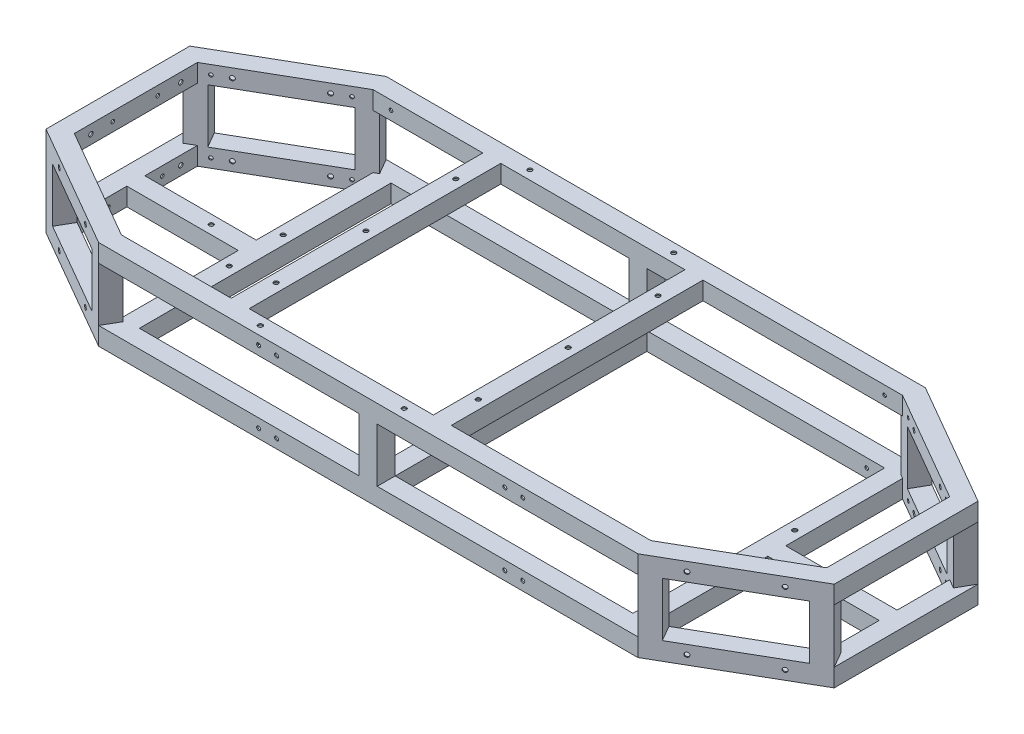
SolidWorks part; units mm, degrees
material "6061-T6 (SS)"
ref_plane "Front Plane" through (0, 0, 0) normal (0, 0, 1) x (1, 0, 0)
ref_plane "Top Plane" through (0, 0, 0) normal (0, 1, 0) x (1, 0, 0)
ref_plane "Right Plane" through (0, 0, 0) normal (1, 0, 0) x (0, 0, -1)
sketch "Sketch2" plane through (0, 0, 0) normal (1, 0, 0) x (0, 0, -1)
  line L0 (179.451, -11.049) -> (179.451, 11.049)
  line L5 (179.451, 11.049) -> (201.549, 11.049)
  line L6 (201.549, -11.049) -> (201.549, 11.049)
  line L7 (177.8, -12.7) -> (203.2, -12.7)
  line L8 (177.8, -12.7) -> (177.8, 12.7)
  line L9 (177.8, 12.7) -> (203.2, 12.7)
  line L10 (203.2, -12.7) -> (203.2, 12.7)
  line L11 (177.8, -12.7) -> (203.2, 12.7) construction
  line L12 (177.8, 12.7) -> (203.2, -12.7) construction
  line L13 (179.451, -11.049) -> (201.549, -11.049)
  point P5 (190.5, 0)
  dimension "D1" = 25.4
  dimension "D3" = 203.2
  dimension "D2" = 1.651
sketch "Sketch3" plane through (0, 0, 0) normal (0, 1, 0) x (1, 0, 0)
  line L0 (-381, 203.2) -> (381, 203.2)
  line L1 (0, 177.8) -> (0, 203.2) construction
  line L2 (0, 177.8) -> (0, 203.2) construction
  line L3 (381, 203.2) -> (556.9764, 101.6)
  line L4 (556.9764, 101.6) -> (556.9764, -101.6)
  line L5 (556.9764, -101.6) -> (381, -203.2)
  line L8 (381, -203.2) -> (-381, -203.2)
  line L9 (0, -203.2) -> (0, 203.2) construction
  line L10 (0, 0) -> (556.9764, 0) construction
  line L11 (-556.9764, -101.6) -> (-381, -203.2)
  line L12 (-556.9764, 101.6) -> (-556.9764, -101.6)
  line L13 (-381, 203.2) -> (-556.9764, 101.6)
  dimension "D1" = 762
  dimension "D2" = 30
  dimension "D3" = 203.2
  dimension "D4" = 203.2
  dimension "D5" = 203.2
  dimension "D6" = 30
sweep "Bottom Frame" add profiles "Sketch2" path "Sketch3"
sketch "Sketch4" plane through (0, 12.7, 0) normal (0, 1, 0) x (1, 0, 0)
  line L0 (-381, -203.2) -> (-402.997, -190.5)
  line L1 (-381, -203.2) -> (-556.9764, -101.6) construction
  line L2 (-402.997, -190.5) -> (-390.297, -168.503)
  line L3 (-374.1941, -177.8) -> (-531.5764, -86.9353) construction
  line L4 (-390.297, -168.503) -> (-368.3, -181.203)
  line L5 (-368.3, -181.203) -> (-381, -203.2)
  line L6 (-381.6043, -200.9447) -> (-400.7417, -189.8957)
  line L7 (-400.7417, -189.8957) -> (-389.6927, -170.7583)
  line L8 (-389.6927, -170.7583) -> (-370.5553, -181.8073)
  line L9 (-370.5553, -181.8073) -> (-381.6043, -200.9447)
  dimension "D2" = 1.651
  dimension "D1" = 25.4
extrude "Vertical Member 1" add sketch "Sketch4" along normal blind 76.2
sketch "Sketch5" plane through (0, 12.7, 0) normal (0, 1, 0) x (1, 0, 0)
  line L0 (-556.9764, -101.6) -> (-534.9793, -114.3)
  line L1 (-402.997, -190.5) -> (-556.9764, -101.6) construction
  line L2 (-534.9793, -114.3) -> (-522.2793, -92.303)
  line L3 (-390.297, -168.503) -> (-531.5764, -86.9353) construction
  line L4 (-522.2793, -92.303) -> (-544.2764, -79.603)
  line L5 (-544.2764, -79.603) -> (-556.9764, -101.6)
  line L6 (-554.7211, -100.9957) -> (-535.5836, -112.0447)
  line L7 (-535.5836, -112.0447) -> (-524.5346, -92.9073)
  line L8 (-524.5346, -92.9073) -> (-543.6721, -81.8583)
  line L9 (-543.6721, -81.8583) -> (-554.7211, -100.9957)
  dimension "D2" = 1.651
  dimension "D1" = 25.4
extrude "Vertical Member 2" add sketch "Sketch5" along normal blind 76.2
mirror "Vertical Member 3 & 4" about plane through (0, 0, 0) normal (0, 0, 1) of "Vertical Member 1", "Vertical Member 2"
mirror "Vertical Members 5, 6, 7, 8" about plane through (0, 0, 0) normal (1, 0, 0) of "Vertical Member 3 & 4", "Vertical Member 1", "Vertical Member 2"
sketch "Sketch6" plane through (0, 12.7, 0) normal (0, 1, 0) x (1, 0, 0)
  line L0 (0, 0) -> (0, -203.2) construction
  line L1 (381, -203.2) -> (-381, -203.2) construction
  line L8 (374.1941, -177.8) -> (-374.1941, -177.8) construction
  line L9 (-12.7, -203.2) -> (12.7, -203.2)
  line L10 (-12.7, -203.2) -> (-12.7, -177.8)
  line L11 (-12.7, -177.8) -> (12.7, -177.8)
  line L12 (12.7, -203.2) -> (12.7, -177.8)
  line L13 (-11.049, -201.549) -> (-11.049, -179.451)
  line L14 (-11.049, -179.451) -> (11.049, -179.451)
  line L15 (11.049, -201.549) -> (11.049, -179.451)
  line L16 (-11.049, -201.549) -> (11.049, -201.549)
  point P11 (0, -203.2)
  dimension "D2" = 1.651
  dimension "D1" = 25.4
extrude "Middle Vertical Member 1" add sketch "Sketch6" along normal blind 88.9
mirror "Middle Vertical Member 2" about plane through (0, 0, 0) normal (0, 0, 1) of "Middle Vertical Member 1"
ref_plane "Top Frame Mirror Plane" through (0, 50.8, 0) normal (0, 1, 0) x (1, 0, 0)
mirror "Top Frame" about plane through (0, 50.8, 0) normal (0, 1, 0) of "Bottom Frame"
sketch "Sketch7" plane through (0, 0, 177.8) normal (0, 0, -1) x (-1, 0, 0)
  line L7 (12.7, 88.9) -> (12.7, 12.7) construction
  line L8 (-12.7, 12.7) -> (12.7, 12.7)
  line L9 (-12.7, 12.7) -> (-12.7, -12.7)
  line L10 (-12.7, -12.7) -> (12.7, -12.7)
  line L11 (12.7, 12.7) -> (12.7, -12.7)
  line L12 (-11.049, 11.049) -> (-11.049, -11.049)
  line L13 (-11.049, -11.049) -> (11.049, -11.049)
  line L14 (11.049, 11.049) -> (11.049, -11.049)
  line L15 (-11.049, 11.049) -> (11.049, 11.049)
  dimension "D2" = 1.651
  dimension "D1" = 25.4
extrude "Middle Support" add sketch "Sketch7" along normal up to surface (355.6 mm away)
sketch "Sketch8" plane through (0, 0, 177.8) normal (0, 0, -1) x (-1, 0, 0)
  line L0 (12.7, -12.7) -> (374.1941, -12.7) construction
  line L1 (374.1941, 12.7) -> (348.7941, 12.7)
  line L2 (374.1941, 12.7) -> (374.1941, -12.7)
  line L3 (374.1941, -12.7) -> (348.7941, -12.7)
  line L4 (348.7941, 12.7) -> (348.7941, -12.7)
  line L5 (372.5431, 11.049) -> (372.5431, -11.049)
  line L6 (372.5431, -11.049) -> (350.4451, -11.049)
  line L7 (350.4451, 11.049) -> (350.4451, -11.049)
  line L8 (372.5431, 11.049) -> (350.4451, 11.049)
  dimension "D2" = 1.651
  dimension "D1" = 25.4
extrude "Bottom Support Rear" add sketch "Sketch8" along normal up to surface (355.6 mm away) up to face at (193.447, 0, -177.8)
sketch "Sketch9" plane through (-531.5764, 0, 0) normal (1, 0, 0) x (0, 0, -1)
  line L0 (-86.9353, 12.7) -> (86.9353, 12.7) construction
  line L1 (-12.7, 12.7) -> (12.7, 12.7)
  line L2 (-12.7, 12.7) -> (-12.7, -12.7)
  line L3 (-12.7, -12.7) -> (12.7, -12.7)
  line L4 (12.7, 12.7) -> (12.7, -12.7)
  line L5 (-86.9353, -12.7) -> (86.9353, -12.7) construction
  line L6 (-11.049, 11.049) -> (-11.049, -11.049)
  line L7 (-11.049, -11.049) -> (11.049, -11.049)
  line L8 (11.049, 11.049) -> (11.049, -11.049)
  line L9 (-11.049, 11.049) -> (11.049, 11.049)
  point P6 (0, -12.7)
  dimension "D2" = 1.651
  dimension "D1" = 25.4
extrude "I Beam" add sketch "Sketch9" along normal up to surface (157.3823 mm away) up to face at (-374.1941, 0, 0)
mirror "Bottom Support Front w/ I Beam" about plane through (0, 0, 0) normal (1, 0, 0) of "Bottom Support Rear", "I Beam"
sketch "Sketch10" plane through (0, 0, 177.8) normal (0, 0, -1) x (-1, 0, 0)
  line L0 (195.326, 90.551) -> (195.326, 112.649)
  line L1 (193.675, 88.9) -> (219.075, 88.9)
  line L2 (193.675, 88.9) -> (193.675, 114.3)
  line L3 (193.675, 114.3) -> (219.075, 114.3)
  line L4 (219.075, 88.9) -> (219.075, 114.3)
  line L5 (193.675, 88.9) -> (219.075, 114.3) construction
  line L6 (193.675, 114.3) -> (219.075, 88.9) construction
  line L7 (195.326, 112.649) -> (217.424, 112.649)
  line L8 (217.424, 90.551) -> (217.424, 112.649)
  line L9 (195.326, 90.551) -> (217.424, 90.551)
  line L10 (374.1941, 114.3) -> (-374.1941, 114.3) construction
  line L11 (374.1941, 88.9) -> (12.7, 88.9) construction
  point P0 (206.375, 101.6)
  dimension "D2" = 1.651
  dimension "D1" = 25.4
  dimension "D3" = 206.375
extrude "Top Rear Support" add sketch "Sketch10" along normal up to surface (355.6 mm away) up to face at (180.747, 0, -177.8)
ref_plane "Top Support Plane" through (-63.5, 0, 0) normal (1, 0, 0) x (0, 0, -1)
mirror "Top Front Support" about plane through (-63.5, 0, 0) normal (1, 0, 0) of "Top Rear Support"
sketch "Top Rear Support Holes" plane through (0, 114.3, 0) normal (0, 1, 0) x (1, 0, 0)
  line L0 (-206.375, 127) -> (-206.375, -127) construction
  line L1 (-219.075, 177.8) -> (-219.075, -177.8) construction
  point P4 (-206.375, 0)
  point P5 (-219.075, 0)
  dimension "D1" = 254
  dimension "D2" = 12.7
hole_wizard "1/4 (0.25) Diameter Hole 1" positions "Sketch12" profile "Sketch13" hole size "1/4" standard "ANSI Inch" end condition through all
sketch "Sketch12" plane through (0, 114.3, 0) normal (0, 1, 0) x (1, 0, 0)
  point P0 (-206.375, 127)
  point P3 (-206.375, -127)
  point P6 (-206.375, 0)
sketch "Sketch13" plane through (-206.375, 114.3, -127) normal (1, 0, 0) x (0, 0, 1)
  line L0 (0, 0) -> (0, 127)
  line L1 (0, 127) -> (3.175, 127)
  line L2 (3.175, 127) -> (3.175, 0)
  line L5 (3.175, 0) -> (0, 0)
  line L11 (0, -6.35) -> (0, 107.95) construction
  dimension "Thru Hole Dia." = 6.35
  dimension "Thru Hole Depth" = 127
mirror "1/4 (0.25) Diameter Hole 2" about plane through (-63.5, 0, 0) normal (1, 0, 0) of "1/4 (0.25) Diameter Hole 1"
sketch "Right SIde Holes" plane through (0, 114.3, 0) normal (0, 1, 0) x (1, 0, 0)
  line L0 (-165.1, -190.5) -> (38.1, -190.5) construction
  line L1 (-193.675, -177.8) -> (66.675, -177.8) construction
  point P2 (-63.5, -190.5)
  dimension "D1" = 203.2
  dimension "D2" = 63.5
  dimension "D3" = 12.7
hole_wizard "1/4 (0.25) Diameter Hole 3" positions "Sketch15" profile "Sketch17" hole size "1/4" standard "ANSI Inch"
sketch "Sketch15" plane through (0, 114.3, 0) normal (0, 1, 0) x (1, 0, 0)
  point P0 (-165.1, -190.5)
  point P3 (38.1, -190.5)
sketch "Sketch17" plane through (-165.1, 114.3, 190.5) normal (1, 0, 0) x (0, 0, 1)
  line L0 (0, 0) -> (0, 52.7077)
  line L1 (0, 52.7077) -> (3.175, 50.8)
  line L2 (3.175, 50.8) -> (3.175, 0)
  line L5 (3.175, 0) -> (0, 0)
  line L10 (0, 52.7077) -> (-3.175, 50.8) construction
  line L11 (0, -6.35) -> (0, 107.95) construction
  dimension "Hole Dia." = 6.35
  dimension "Hole Depth" = 50.8
  dimension "Drill Angle" = 118
mirror "1/4 (0.25) Diameter Hole 4" about plane through (0, 0, 0) normal (0, 0, 1) of "1/4 (0.25) Diameter Hole 3"
sketch "Hole Location" plane through (-183.2382, 0, 317.3778) normal (-0.5, 0, 0.866) x (0.866, 0, 0.5)
  line L0 (-380.7557, 101.6) -> (-279.1557, 101.6) construction
  line L1 (-406.1557, 88.9) -> (-253.7557, 88.9) construction
  point P4 (-329.9557, 101.6)
  point P5 (-329.9557, 88.9)
  dimension "D1" = 101.6
  dimension "D2" = 12.7
hole_wizard "1/4 (0.25) Diameter Hole3" positions "Sketch19" profile "Sketch20" hole size "1/4" standard "ANSI Inch"
sketch "Sketch19" plane through (-183.2382, 0, 317.3778) normal (-0.5, 0, 0.866) x (0.866, 0, 0.5)
  point P0 (-380.7557, 101.6)
  point P3 (-279.1557, 101.6)
sketch "Sketch20" plane through (-512.9823, 101.6, 127) normal (0, 1, 0) x (0.866, 0, 0.5)
  line L0 (0, 0) -> (0, 52.7077)
  line L1 (0, 52.7077) -> (3.175, 50.8)
  line L2 (3.175, 50.8) -> (3.175, 0)
  line L5 (3.175, 0) -> (0, 0)
  line L10 (0, 52.7077) -> (-3.175, 50.8) construction
  line L11 (0, -6.35) -> (0, 107.95) construction
  dimension "Hole Dia." = 6.35
  dimension "Hole Depth" = 50.8
  dimension "Drill Angle" = 118
mirror "Hole Location 1" about plane through (0, 50.8, 0) normal (0, 1, 0) of "1/4 (0.25) Diameter Hole3"
mirror "Hole Location 2" about plane through (0, 0, 0) normal (0, 0, 1) of "Hole Location 1", "1/4 (0.25) Diameter Hole3"
mirror "Hole Location 3" about plane through (0, 0, 0) normal (1, 0, 0) of "Hole Location 2", "1/4 (0.25) Diameter Hole3", "Hole Location 1"
sketch "Sketch22" plane through (-170.5382, 0, -295.3808) normal (0.5, 0, 0.866) x (0.866, 0, -0.5)
  line L0 (-402.9807, 101.6) -> (-256.9307, 101.6) construction
  line L2 (-329.9557, 88.9) -> (-329.9557, 114.3) construction
  line L3 (-253.7557, 88.9) -> (-406.1557, 88.9) construction
  line L4 (-235.1616, 114.3) -> (-416.891, 114.3) construction
  circle A0 centre (-402.9807, 101.6) radius 2.54
  circle A1 centre (-256.9307, 101.6) radius 2.54
  point P9 (-329.9557, 101.6)
  dimension "D2" = 5.08
  dimension "D3" = 5.08
  dimension "D1" = 146.05
extrude "Inner Hole Location 1" cut sketch "Sketch22" against normal blind 6.35
mirror "Inner Hole Location 2" about plane through (0, 50.8, 0) normal (0, 1, 0) of "Inner Hole Location 1"
mirror "Inner Hole Location 3" about plane through (0, 0, 0) normal (0, 0, 1) of "Inner Hole Location 2", "Inner Hole Location 1"
mirror "Inner Hole Location 4" about plane through (0, 0, 0) normal (1, 0, 0) of "Inner Hole Location 3", "Inner Hole Location 1", "Inner Hole Location 2"
sketch "Sketch23" plane through (0, 12.7, 0) normal (0, 1, 0) x (1, 0, 0)
  line L1 (-374.1941, 12.7) -> (-531.5764, 12.7) construction
  line L2 (-374.1941, 177.8) -> (-374.1941, 12.7) construction
  line L3 (-374.1941, -177.8) -> (-219.075, -177.8) construction
  line L4 (-374.1941, -12.7) -> (-374.1941, -177.8) construction
  circle A0 centre (-424.9941, 0) radius 3.175
  circle A1 centre (-361.4941, -38.1) radius 3.175
  circle A2 centre (-361.4941, 38.1) radius 3.175
  dimension "D1" = 6.35
  dimension "D2" = 12.7
  dimension "D3" = 50.8
  dimension "D4" = 139.7
  dimension "D5" = 215.9
  dimension "D6" = 12.7
  dimension "D7" = 12.7
extrude "Rear Shock Mount Holes" cut sketch "Sketch23" against normal through all
mirror "Front Shock Mount Holes" about plane through (0, 0, 0) normal (1, 0, 0) of "Rear Shock Mount Holes"
sketch "Sketch24" plane through (0, 88.9, 0) normal (0, -1, 0) x (1, 0, 0)
  line L0 (-206.375, 130.175) -> (-206.375, 123.825) construction
  line L1 (-193.675, 177.8) -> (-12.7, 177.8) construction
  line L2 (-206.375, 3.175) -> (-206.375, -3.175) construction
  line L3 (-12.7, -177.8) -> (-193.675, -177.8) construction
  line L4 (-206.375, -123.825) -> (-206.375, -130.175) construction
  line L5 (66.675, 0) -> (-193.675, 0) construction
  line L6 (66.675, -177.8) -> (66.675, 177.8) construction
  line L7 (-193.675, -177.8) -> (-193.675, 177.8) construction
  line L8 (-63.5, 0) -> (-63.5, 177.8) construction
  circle A0 centre (-206.375, 139.7) radius 1.2446
  circle A1 centre (-206.375, 114.3) radius 1.2446
  circle A2 centre (-206.375, 127) radius 3.175 construction
  circle A3 centre (-206.375, 12.7) radius 1.2446
  circle A4 centre (-206.375, -12.7) radius 1.2446
  circle A5 centre (-206.375, 0) radius 3.175 construction
  circle A6 centre (-206.375, -114.3) radius 1.2446
  circle A7 centre (-206.375, -139.7) radius 1.2446
  circle A8 centre (-206.375, -127) radius 3.175 construction
  circle A9 centre (79.375, 139.7) radius 1.2446
  circle A10 centre (79.375, 114.3) radius 1.2446
  circle A11 centre (79.375, 12.7) radius 1.2446
  circle A12 centre (79.375, -12.7) radius 1.2446
  circle A13 centre (79.375, -114.3) radius 1.2446
  circle A14 centre (79.375, -139.7) radius 1.2446
  dimension "D1" = 2.4892
  dimension "D2" = 38.1
  dimension "D3" = 25.4
  dimension "D4" = 101.6
  dimension "D5" = 25.4
  dimension "D6" = 38.1
  dimension "D7" = 25.4
extrude "Z Direction Holes" cut sketch "Sketch24" against normal blind 1.651
sketch "Sketch25" plane through (0, 88.9, 0) normal (0, -1, 0) x (1, 0, 0)
  line L0 (-168.275, -190.5) -> (-161.925, -190.5) construction
  line L1 (66.675, 0) -> (-193.675, 0) construction
  line L2 (66.675, -177.8) -> (66.675, 177.8) construction
  line L3 (-193.675, -177.8) -> (-193.675, 177.8) construction
  line L4 (-63.5, 0) -> (-63.5, -177.8) construction
  line L5 (-12.7, -177.8) -> (-193.675, -177.8) construction
  circle A0 centre (-152.4, -190.5) radius 1.2446
  circle A1 centre (-177.8, -190.5) radius 1.2446
  circle A2 centre (-165.1, -190.5) radius 3.175 construction
  circle A3 centre (50.8, -190.5) radius 1.2446
  circle A4 centre (25.4, -190.5) radius 1.2446
  circle A5 centre (50.8, 190.5) radius 1.2446
  circle A6 centre (25.4, 190.5) radius 1.2446
  circle A7 centre (-177.8, 190.5) radius 1.2446
  circle A8 centre (-152.4, 190.5) radius 1.2446
  dimension "D1" = 2.4892
  dimension "D2" = 203.2
  dimension "D3" = 25.4
extrude "X Direction Holes" cut sketch "Sketch25" against normal blind 1.651
sketch "Sketch26" plane through (-556.9764, 0, 0) normal (-1, 0, 0) x (0, 0, 1)
  line L0 (-101.6, 88.9) -> (-101.6, 114.3) construction
  line L1 (-101.6, 114.3) -> (101.6, 114.3) construction
  line L2 (-101.6, 50.8) -> (101.6, 50.8) construction
  line L3 (-101.6, 88.9) -> (-101.6, 12.7) construction
  line L4 (101.6, 88.9) -> (101.6, 12.7) construction
  circle A0 centre (-63.5, 101.6) radius 3.175
  circle A1 centre (63.5, 101.6) radius 3.175
  circle A4 centre (63.5, 0) radius 3.175
  circle A5 centre (-63.5, 0) radius 3.175
  dimension "D1" = 6.35
  dimension "D2" = 38.1
  dimension "D3" = 127
  dimension "D4" = 12.7
extrude "Rear Holes" cut sketch "Sketch26" against normal blind 25.4
sketch "Sketch27" plane through (0, -12.7, 0) normal (0, -1, 0) x (1, 0, 0)
  line L1 (-348.7941, -177.8) -> (-348.7941, -203.2) construction
  line L4 (-381, -203.2) -> (381, -203.2) construction
  line L5 (-531.5764, -86.9353) -> (-556.9764, -86.9353) construction
  line L6 (-556.9764, 101.6) -> (-556.9764, -101.6) construction
  line L7 (531.5764, -86.9353) -> (556.9764, -86.9353) construction
  line L8 (556.9764, -101.6) -> (556.9764, 101.6) construction
  line L9 (-556.9764, 0) -> (556.9764, 0) construction
  circle A0 centre (-361.442, -190.5) radius 1.2446
  circle A1 centre (-243.078, -190.5) radius 1.2446
  circle A2 centre (-121.666, -190.5) radius 1.2446
  circle A3 centre (0, -190.5) radius 1.2446
  circle A4 centre (121.666, -190.5) radius 1.2446
  circle A5 centre (243.078, -190.5) radius 1.2446
  circle A6 centre (361.442, -190.5) radius 1.2446
  circle A7 centre (-544.2764, -94.234) radius 1.2446
  circle A8 centre (544.2764, -94.234) radius 1.2446
  circle A9 centre (544.2764, 94.234) radius 1.2446
  circle A10 centre (361.442, 190.5) radius 1.2446
  circle A11 centre (243.078, 190.5) radius 1.2446
  circle A12 centre (121.666, 190.5) radius 1.2446
  circle A13 centre (0, 190.5) radius 1.2446
  circle A14 centre (-121.666, 190.5) radius 1.2446
  circle A15 centre (-243.078, 190.5) radius 1.2446
  circle A16 centre (-361.442, 190.5) radius 1.2446
  circle A17 centre (-544.2764, 94.234) radius 1.2446
  point P20 (-348.7941, -190.5)
  point P29 (-544.2764, -86.9353)
  point P38 (544.2764, -86.9353)
  dimension "D1" = 2.4892
  dimension "D2" = 19.558
  dimension "D3" = 137.922
  dimension "D4" = 259.334
  dimension "D5" = 381
  dimension "D6" = 502.666
  dimension "D7" = 624.078
  dimension "D8" = 19.558
  dimension "D9" = 7.366
  dimension "D10" = 7.366
extrude "Cut-Extrude5" cut sketch "Sketch27" against normal blind 1.651
sketch "Sketch28" [suppressed] plane through (0, 0, -203.2) normal (0, 0, -1) x (-1, 0, 0)
  line L0 (-381, 101.6) -> (381, 101.6) construction
  line L1 (-381, 88.9) -> (-381, 114.3) construction
  line L2 (381, 88.9) -> (381, 114.3) construction
  line L3 (-381, 0) -> (381, 0) construction
  line L4 (-381, -12.7) -> (-381, 12.7) construction
  line L5 (381, -12.7) -> (381, 12.7) construction
  circle A0 centre (-252.73, 101.6) radius 3.3782
  circle A1 centre (-193.04, 101.6) radius 3.3782
  circle A2 centre (-218.44, 101.6) radius 3.3782
  circle A3 centre (-252.73, 0) radius 3.3782
  circle A4 centre (-218.44, 0) radius 3.3782
  circle A5 centre (-193.04, 0) radius 3.3782
  circle A6 centre (129.54, 101.6) radius 3.3782
  circle A7 centre (154.94, 101.6) radius 3.3782
  circle A8 centre (176.53, 101.6) radius 3.3782
  circle A9 centre (129.54, 0) radius 3.3782
  circle A10 centre (154.94, 0) radius 3.3782
  circle A11 centre (176.53, 0) radius 3.3782
  dimension "D4" = 6.7564
  dimension "D1" = 128.27
  dimension "D2" = 162.56
  dimension "D3" = 187.96
  dimension "D5" = 510.54
  dimension "D6" = 535.94
  dimension "D7" = 557.53
extrude "Cut-Extrude6" [suppressed] cut sketch "Sketch28" against normal blind 25.4
sketch "Sketch29" plane through (0, 0, 203.2) normal (0, 0, 1) x (1, 0, 0)
  line L0 (-381, 101.6) -> (381, 101.6) construction
  line L1 (-381, 88.9) -> (-381, 114.3) construction
  line L2 (381, 88.9) -> (381, 114.3) construction
  line L3 (-381, 0) -> (381, 0) construction
  line L4 (-381, -12.7) -> (-381, 12.7) construction
  line L5 (381, -12.7) -> (381, 12.7) construction
  circle A1 centre (-154.94, 101.6) radius 2.8067
  circle A2 centre (-129.54, 101.6) radius 2.8067
  circle A4 centre (-154.94, 0) radius 2.8067
  circle A5 centre (-129.54, 0) radius 2.8067
  circle A6 centre (193.04, 101.6) radius 2.8067
  circle A7 centre (218.44, 101.6) radius 2.8067
  circle A9 centre (193.04, 0) radius 2.8067
  circle A10 centre (218.44, 0) radius 2.8067
  dimension "D1" = 5.6134
  dimension "D3" = 226.06
  dimension "D4" = 251.46
  dimension "D5" = 574.04
  dimension "D6" = 599.44
extrude "Cut-Extrude7" cut sketch "Sketch29" against normal blind 25.4
sketch "Sketch30" plane through (0, 0, -177.8) normal (0, 0, 1) x (1, 0, 0)
  line L0 (374.1941, 114.3) -> (92.075, 114.3) construction
  line L1 (374.1941, 88.9) -> (374.1941, 114.3) construction
  line L2 (-219.075, 114.3) -> (-374.1941, 114.3) construction
  line L3 (-374.1941, 88.9) -> (-374.1941, 114.3) construction
  line L4 (-348.7941, -12.7) -> (-12.7, -12.7) construction
  line L5 (12.7, -12.7) -> (348.7941, -12.7) construction
  circle A0 centre (348.7941, 101.6) radius 2.54
  circle A1 centre (-348.7941, 101.6) radius 2.54
  circle A2 centre (-323.3941, 0) radius 2.54
  circle A3 centre (323.3941, 0) radius 2.54
  dimension "D1" = 5.08
  dimension "D2" = 12.7
  dimension "D3" = 25.4
  dimension "D4" = 12.7
  dimension "D5" = 25.4
  dimension "D6" = 50.8
  dimension "D7" = 12.7
  dimension "D8" = 50.8
  dimension "D9" = 12.7
extrude "Cut-Extrude8" cut sketch "Sketch30" against normal blind 1.651
mirror "Mirror1" about plane through (0, 0, 0) normal (0, 0, 1) of "Cut-Extrude8"
sketch "Sketch31" plane through (-531.5764, 0, 0) normal (1, 0, 0) x (0, 0, -1)
  line L0 (86.9353, 114.3) -> (-86.9353, 114.3) construction
  line L1 (-86.9353, 88.9) -> (-86.9353, 114.3) construction
  line L2 (-86.9353, 12.7) -> (-12.7, 12.7) construction
  line L3 (12.7, 12.7) -> (86.9353, 12.7) construction
  line L4 (-86.9353, -12.7) -> (-86.9353, 12.7) construction
  circle A0 centre (-32.5793, 101.6) radius 2.54
  circle A1 centre (30.9207, 101.6) radius 2.54
  circle A2 centre (-38.9293, 0) radius 2.54
  circle A3 centre (37.2707, 0) radius 2.54
  dimension "D1" = 5.08
  dimension "D2" = 12.7
  dimension "D3" = 54.356
  dimension "D4" = 63.5
  dimension "D5" = 12.7
  dimension "D6" = 12.7
  dimension "D7" = 12.7
  dimension "D8" = 48.006
  dimension "D9" = 76.2
extrude "Cut-Extrude9" cut sketch "Sketch31" against normal blind 1.651
mirror "Mirror2" about plane through (0, 0, 0) normal (1, 0, 0) of "Cut-Extrude9"
sketch "Sketch32" plane through (0, 114.3, 0) normal (0, 1, 0) x (1, 0, 0)
  line L0 (-219.075, 177.8) -> (-219.075, -177.8) construction
  line L1 (381, 203.2) -> (-381, 203.2) construction
  line L2 (-348.7941, 0) -> (-219.075, 0) construction
  line L3 (-348.7941, 177.8) -> (-348.7941, -177.8) construction
  circle A0 centre (-283.972, 190.5) radius 6.35
  circle A1 centre (-283.972, -190.5) radius 6.35
  dimension "D1" = 12.7
  dimension "D2" = 64.897
  dimension "D3" = 12.7
extrude "Cut-Extrude10" [suppressed] cut sketch "Sketch32" against normal through all
equation "\"Tubing\"= 1in"
equation "\"Wall Thickness\"= 0.065"
equation "\"D1@Sketch2\" = \"Tubing\""
equation "\"D2@Sketch2\"= \"Wall Thickness\""
equation "\"D1@Sketch4\"= \"Tubing\""
equation "\"D2@Sketch4\"= \"Wall Thickness\""
equation "\"D1@Sketch5\"= \"Tubing\""
equation "\"D2@Sketch5\"= \"Wall Thickness\""
equation "\"D1@Sketch6\"= \"Tubing\""
equation "\"D2@Sketch6\"= \"Wall Thickness\""
equation "\"D1@Sketch7\"= \"Tubing\""
equation "\"D2@Sketch7\"= \"Wall Thickness\""
equation "\"D1@Sketch8\"= \"Tubing\""
equation "\"D2@Sketch8\"= \"Wall Thickness\""
equation "\"D1@Sketch9\"= \"Tubing\""
equation "\"D2@Sketch9\"= \"Wall Thickness\""
equation "\"D1@Sketch10\"= \"Tubing\""
equation "\"D2@Sketch10\"= \"Wall Thickness\""
